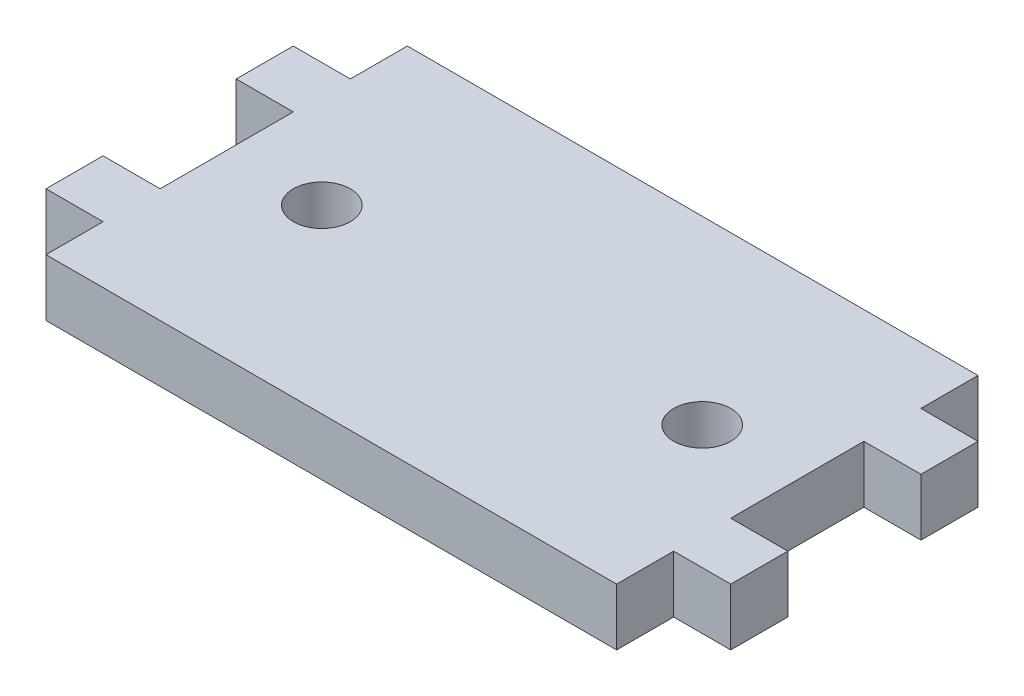
SolidWorks part; units mm, degrees
ref_plane "Front Plane" through (0, 0, 0) normal (0, 0, 1) x (1, 0, 0)
ref_plane "Top Plane" through (0, 0, 0) normal (0, 1, 0) x (1, 0, 0)
ref_plane "Right Plane" through (0, 0, 0) normal (1, 0, 0) x (0, 0, -1)
sketch "Sketch1" plane through (0, 0, 0) normal (0, 1, 0) x (1, 0, 0)
  line L0 (-42.8674, 7) -> (-42.8674, 10)
  line L1 (-42.8674, 10) -> (-39.8674, 10)
  line L2 (-39.8674, 10) -> (-39.8674, 13)
  line L3 (-39.8674, 13) -> (-9.8674, 13)
  line L4 (-9.8674, 13) -> (-9.8674, 10)
  line L5 (-9.8674, 10) -> (-6.8674, 10)
  line L6 (-6.8674, 10) -> (-6.8674, 7)
  line L7 (-6.8674, 7) -> (-9.8674, 7)
  line L8 (-9.8674, 7) -> (-9.8674, 0)
  line L9 (-9.8674, 0) -> (-6.8674, 0)
  line L10 (-6.8674, 0) -> (-6.8674, -3)
  line L11 (-6.8674, -3) -> (-9.8674, -3)
  line L12 (-9.8674, -3) -> (-9.8674, -6)
  line L13 (-9.8674, -6) -> (-39.8674, -6)
  line L14 (-39.8674, -6) -> (-39.8674, -3)
  line L15 (-39.8674, -3) -> (-42.8674, -3)
  line L16 (-42.8674, -3) -> (-42.8674, 0)
  line L17 (-42.8674, 0) -> (-39.8674, 0)
  line L18 (-39.8674, 0) -> (-39.8674, 7)
  line L19 (-39.8674, 7) -> (-42.8674, 7)
  line L20 (-24.8674, 13) -> (-24.8674, 3.5) construction
  line L21 (-24.8674, 3.5) -> (-34.8674, 3.5) construction
  circle A0 centre (-34.8674, 3.5) radius 1.5
  circle A1 centre (-14.8674, 3.5) radius 1.5
  dimension "D6" = 10
  dimension "D7" = 3
  dimension "D1" = 3
  dimension "D2" = 3
  dimension "D3" = 30
  dimension "D4" = 7
  dimension "D5" = 3
extrude "Boss-Extrude1" add sketch "Sketch1" along normal blind 3
